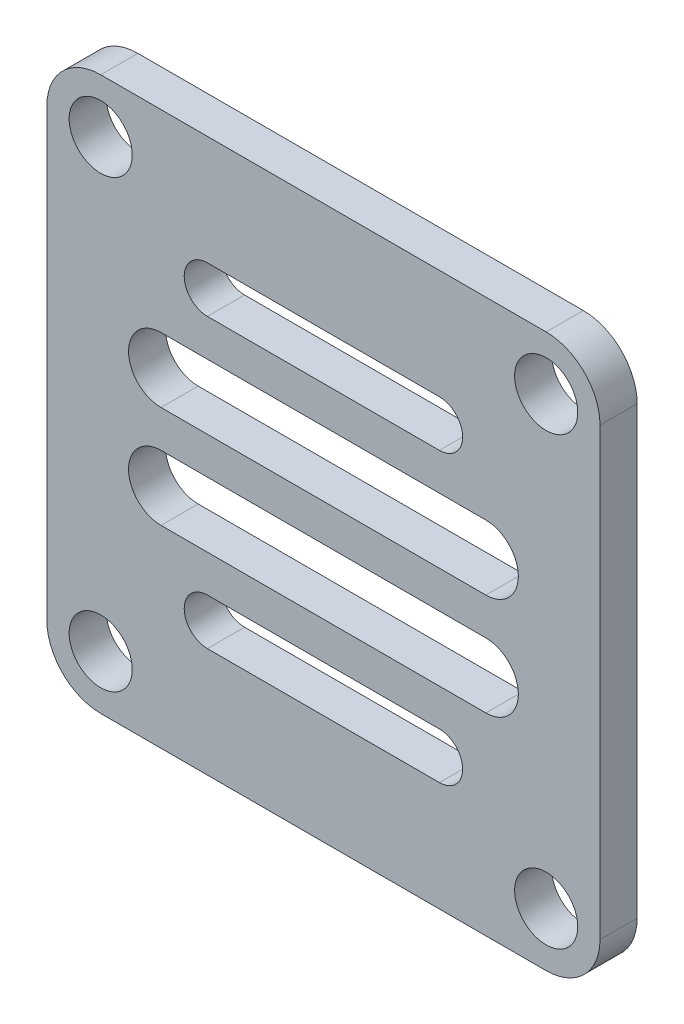
SolidWorks part; units mm, degrees
ref_plane "Front" through (0, 0, 0) normal (0, 0, 1) x (1, 0, 0)
ref_plane "Top" through (0, 0, 0) normal (0, 1, 0) x (1, 0, 0)
ref_plane "Right" through (0, 0, 0) normal (1, 0, 0) x (0, 0, -1)
sketch "Sketch1" plane through (0, 0, 0) normal (0, 0, 1) x (1, 0, 0)
  line L0 (-2.6, -10.5) -> (-2.6, 13.5)
  line L9 (-5.5, -13.4) -> (-29.5, -13.4)
  line L10 (-32.4, -10.5) -> (-32.4, 13.5)
  line L11 (-5.5, 16.4) -> (-29.5, 16.4)
  circle A0 centre (-5.5, -10.5) radius 1.7 construction
  circle A1 centre (-29.5, -10.5) radius 1.7 construction
  circle A2 centre (-29.5, 13.5) radius 1.7 construction
  circle A3 centre (-5.5, 13.5) radius 1.7 construction
  circle A4 centre (-17.5, 1.5) radius 14.15 construction
  circle A5 centre (-5.5, -10.5) radius 1.7
  circle A6 centre (-29.5, -10.5) radius 1.7
  circle A7 centre (-29.5, 13.5) radius 1.7
  circle A8 centre (-5.5, 13.5) radius 1.7
  circle A9 centre (-17.5, 1.5) radius 14.15
  circle A10 centre (-5.5, -10.5) radius 2.9
  circle A11 centre (-29.5, -10.5) radius 2.9
  circle A12 centre (-29.5, 13.5) radius 2.9
  circle A13 centre (-5.5, 13.5) radius 2.9
  circle A14 centre (-17.5, 1.5) radius 13.15
  point P0 (0, 0)
  point P35 (-29.5, 16.4)
  dimension "D1" = 1.2
  dimension "D2" = 1
extrude "Boss-Extrude1" add sketch "Sketch1" against normal blind 2 contours A13 L11 A12 A9 | A13 A9 A8 | A13 A9 A10 L0 | A12 A9 A7 | A12 L10 A11 A9 | A14 | A13 A9 A12 A11 A10 A14 | A11 L9 A10 A9 | A10 A9 A5 | A9 A11 A6 | A9 A10 | A9 A11 | A9 A12 | A9 A13
sketch "Sketch3" plane through (0, 0, 0) normal (0, 0, 1) x (1, 0, 0)
  line L0 (-23.75, 9.25) -> (-11.25, 9.25) construction
  line L1 (-23.75, 10.5) -> (-11.25, 10.5)
  line L2 (-23.75, 8) -> (-11.25, 8)
  line L3 (-26.25, 4.25) -> (-8.75, 4.25) construction
  line L4 (-26.25, 6) -> (-8.75, 6)
  line L5 (-26.25, 2.5) -> (-8.75, 2.5)
  line L6 (-32.4, 1.5) -> (-2.6, 1.5) construction
  line L7 (-32.4, -10.5) -> (-32.4, 13.5) construction
  line L8 (-2.6, -10.5) -> (-2.6, 13.5) construction
  line L9 (-17.5, 16.4) -> (-17.5, -13.4) construction
  line L10 (-5.5, 16.4) -> (-29.5, 16.4) construction
  line L11 (-5.5, -13.4) -> (-29.5, -13.4) construction
  line L12 (-26.25, -1.25) -> (-8.75, -1.25) construction
  line L13 (-26.25, -3) -> (-8.75, -3)
  line L14 (-26.25, 0.5) -> (-8.75, 0.5)
  line L15 (-23.75, -6.25) -> (-11.25, -6.25) construction
  line L16 (-23.75, -7.5) -> (-11.25, -7.5)
  line L17 (-23.75, -5) -> (-11.25, -5)
  arc A0 (-23.75, 10.5) -> (-23.75, 8) centre (-23.75, 9.25) ccw
  arc A1 (-11.25, 8) -> (-11.25, 10.5) centre (-11.25, 9.25) ccw
  arc A2 (-26.25, 6) -> (-26.25, 2.5) centre (-26.25, 4.25) ccw
  arc A3 (-8.75, 2.5) -> (-8.75, 6) centre (-8.75, 4.25) ccw
  arc A5 (-26.25, -3) -> (-26.25, 0.5) centre (-26.25, -1.25) cw
  arc A6 (-8.75, 0.5) -> (-8.75, -3) centre (-8.75, -1.25) cw
  arc A7 (-23.75, -7.5) -> (-23.75, -5) centre (-23.75, -6.25) cw
  arc A8 (-11.25, -5) -> (-11.25, -7.5) centre (-11.25, -6.25) cw
  point P2 (-17.5, 9.25)
  point P7 (-17.5, 4.25)
  point P26 (0, 0)
  point P27 (0, 0)
  point P30 (-17.5, -1.25)
  point P37 (-17.5, -6.25)
  dimension "D1" = 2
  dimension "D2" = 1
  dimension "D3" = 3.5
  dimension "D4" = 2.5
  dimension "D5" = 17.5
  dimension "D6" = 12.5
extrude "Cut-Extrude1" cut sketch "Sketch3" against normal through all both and the other way through all
